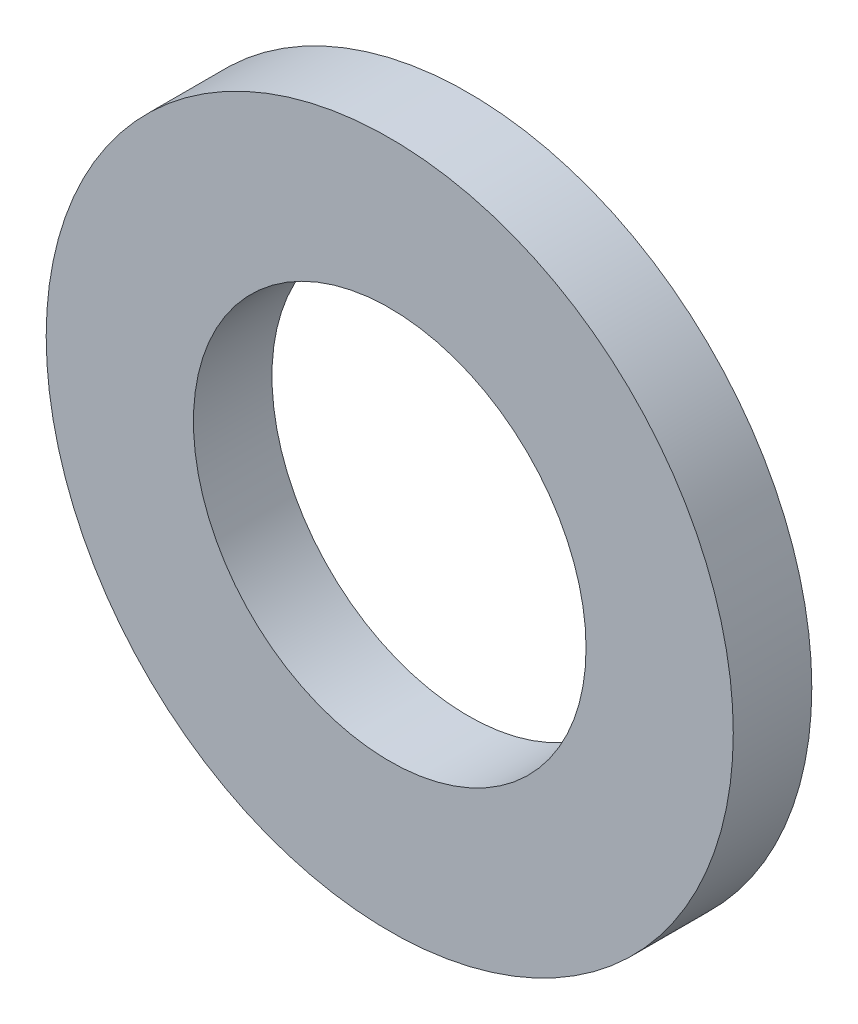
SolidWorks part; units mm, degrees
material "AISI 304"
ref_plane "前视基准面" through (0, 0, 0) normal (0, 0, 1) x (1, 0, 0)
ref_plane "上视基准面" through (0, 0, 0) normal (0, 1, 0) x (1, 0, 0)
ref_plane "右视基准面" through (0, 0, 0) normal (1, 0, 0) x (0, 0, -1)
sketch "草图1" plane through (0, 0, 0) normal (0, 0, 1) x (1, 0, 0)
  circle A0 centre (0, 0) radius 17.5
  circle A1 centre (0, 0) radius 10
  dimension "D1" = 20
  dimension "D2" = 35
extrude "凸台-拉伸1" add sketch "草图1" along normal blind 4
